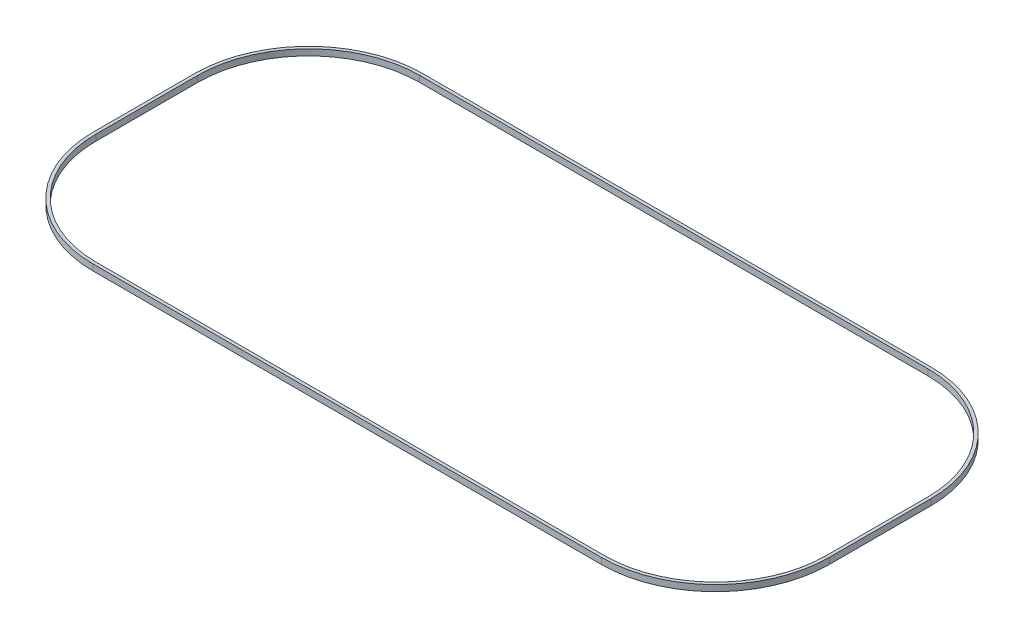
SolidWorks part; units mm, degrees
ref_plane "Front Plane" through (0, 0, 0) normal (0, 0, 1) x (1, 0, 0)
ref_plane "Top Plane" through (0, 0, 0) normal (0, 1, 0) x (1, 0, 0)
ref_plane "Right Plane" through (0, 0, 0) normal (1, 0, 0) x (0, 0, -1)
sketch "Sketch1" plane through (0, 0, 0) normal (0, 1, 0) x (1, 0, 0)
  line L0 (0, 0) -> (83.82, 0)
  line L1 (105.1646, 21.3446) -> (105.1646, 38.1086)
  line L2 (83.82, 59.4532) -> (0, 59.4532)
  line L3 (-21.3446, 38.1086) -> (-21.3446, 21.3446)
  line L4 (0, 3.048) -> (83.82, 3.048)
  line L5 (102.1166, 21.3446) -> (102.1166, 38.1086)
  line L6 (83.82, 56.4052) -> (0, 56.4052)
  line L7 (-18.2966, 38.1086) -> (-18.2966, 21.3446)
  arc A0 (83.82, 0) -> (105.1646, 21.3446) centre (83.82, 21.3446) ccw
  arc A1 (105.1646, 38.1086) -> (83.82, 59.4532) centre (83.82, 38.1086) ccw
  arc A2 (0, 59.4532) -> (-21.3446, 38.1086) centre (0, 38.1086) ccw
  arc A3 (-21.3446, 21.3446) -> (0, 0) centre (0, 21.3446) ccw
  arc A4 (83.82, 3.048) -> (102.1166, 21.3446) centre (83.82, 21.3446) ccw
  arc A5 (102.1166, 38.1086) -> (83.82, 56.4052) centre (83.82, 38.1086) ccw
  arc A6 (0, 56.4052) -> (-18.2966, 38.1086) centre (0, 38.1086) ccw
  arc A7 (-18.2966, 21.3446) -> (0, 3.048) centre (0, 21.3446) ccw
  dimension "D3" = 33.528
  dimension "D4" = 33.528
  dimension "D1" = 83.82
  dimension "D2" = 16.764
  dimension "D5" = 83.82
  dimension "D6" = 33.528
  dimension "D7" = 3.048
extrude "Boss-Extrude1" add sketch "Sketch1" along normal blind 1.016
sketch "Sketch6" plane through (0, 1.016, 0) normal (0, 1, 0) x (1, 0, 0)
  line L0 (0, 0) -> (83.82, 0)
  line L1 (105.1646, 21.3446) -> (105.1646, 38.1086)
  line L2 (83.82, 59.4532) -> (0, 59.4532)
  line L3 (-21.3446, 38.1086) -> (-21.3446, 21.3446)
  line L4 (0, 2.54) -> (83.82, 2.54)
  line L5 (102.6246, 21.3446) -> (102.6246, 38.1086)
  line L6 (83.82, 56.9132) -> (0, 56.9132)
  line L7 (-18.8046, 38.1086) -> (-18.8046, 21.3446)
  arc A0 (83.82, 0) -> (105.1646, 21.3446) centre (83.82, 21.3446) ccw
  arc A1 (105.1646, 38.1086) -> (83.82, 59.4532) centre (83.82, 38.1086) ccw
  arc A2 (0, 59.4532) -> (-21.3446, 38.1086) centre (0, 38.1086) ccw
  arc A3 (-21.3446, 21.3446) -> (0, 0) centre (0, 21.3446) ccw
  arc A4 (83.82, 2.54) -> (102.6246, 21.3446) centre (83.82, 21.3446) ccw
  arc A5 (102.6246, 38.1086) -> (83.82, 56.9132) centre (83.82, 38.1086) ccw
  arc A6 (0, 56.9132) -> (-18.8046, 38.1086) centre (0, 38.1086) ccw
  arc A7 (-18.8046, 21.3446) -> (0, 2.54) centre (0, 21.3446) ccw
  dimension "D3" = 33.528
  dimension "D4" = 33.528
  dimension "D1" = 83.82
  dimension "D2" = 16.764
  dimension "D5" = 83.82
  dimension "D6" = 33.528
  dimension "D7" = 2.54
  dimension "D8" = 0
  dimension "D9" = 0
extrude "Cut-Extrude7" cut sketch "Sketch6" against normal blind 2.54
